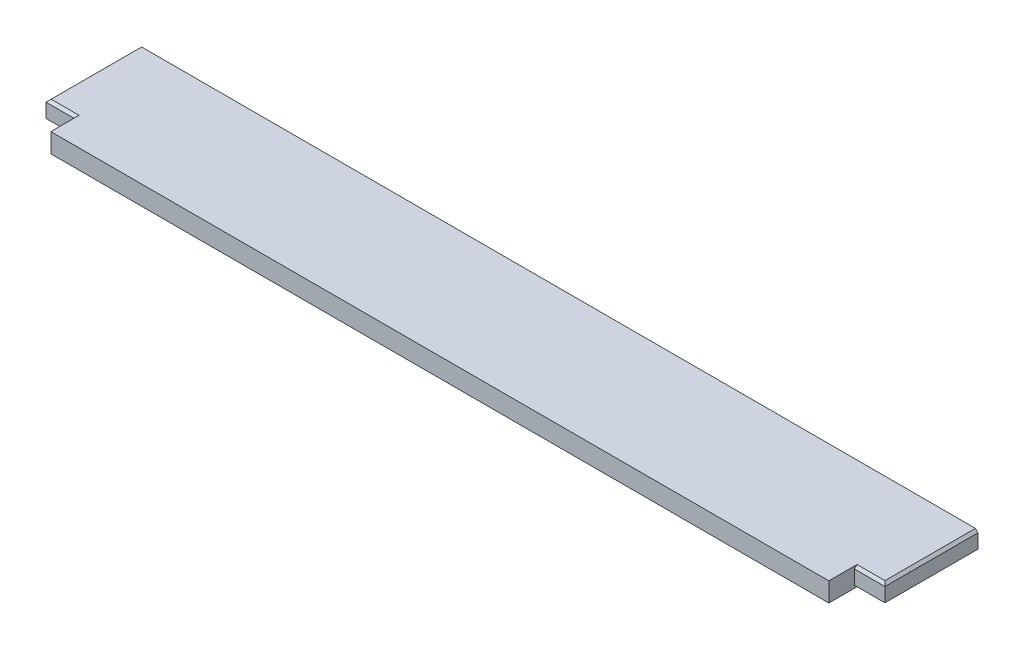
SolidWorks part; units mm, degrees
material "Oak"
ref_plane "Front Plane" through (0, 0, 0) normal (0, 0, 1) x (1, 0, 0)
ref_plane "Top Plane" through (0, 0, 0) normal (0, 1, 0) x (1, 0, 0)
ref_plane "Right Plane" through (0, 0, 0) normal (1, 0, 0) x (0, 0, -1)
sketch "Sketch1" plane through (0, 0, 0) normal (0, 1, 0) x (1, 0, 0)
  line L1 (30.1625, 0) -> (800.1127, 0)
  line L2 (0, 25.4) -> (0, 117.475)
  line L3 (0, 117.475) -> (830.2752, 117.475)
  line L4 (830.2752, 25.4) -> (830.2752, 117.475)
  line L11 (0, 25.4) -> (30.1625, 25.4)
  line L12 (30.1625, 0) -> (30.1625, 25.4)
  line L15 (830.2752, 25.4) -> (800.1127, 25.4)
  line L16 (800.1127, 0) -> (800.1127, 25.4)
  dimension "D1" = 117.475
  dimension "D2" = 830.2752
  dimension "D3" = 30.1625
  dimension "D4" = 30.1625
  dimension "D5" = 25.4
extrude "Boss-Extrude1" add sketch "Sketch1" along normal blind 19.05
chamfer "Chamfer1" distance 2.54 angle 45 8 edges at (830.2752, 19.05, -71.4375) (0, 19.05, -71.4375) (815.194, 19.05, -25.4) (15.0812, 19.05, -25.4) (830.2752, 0, -71.4375) (815.194, 0, -25.4) (15.0812, 0, -25.4) (0, 0, -71.4375)
